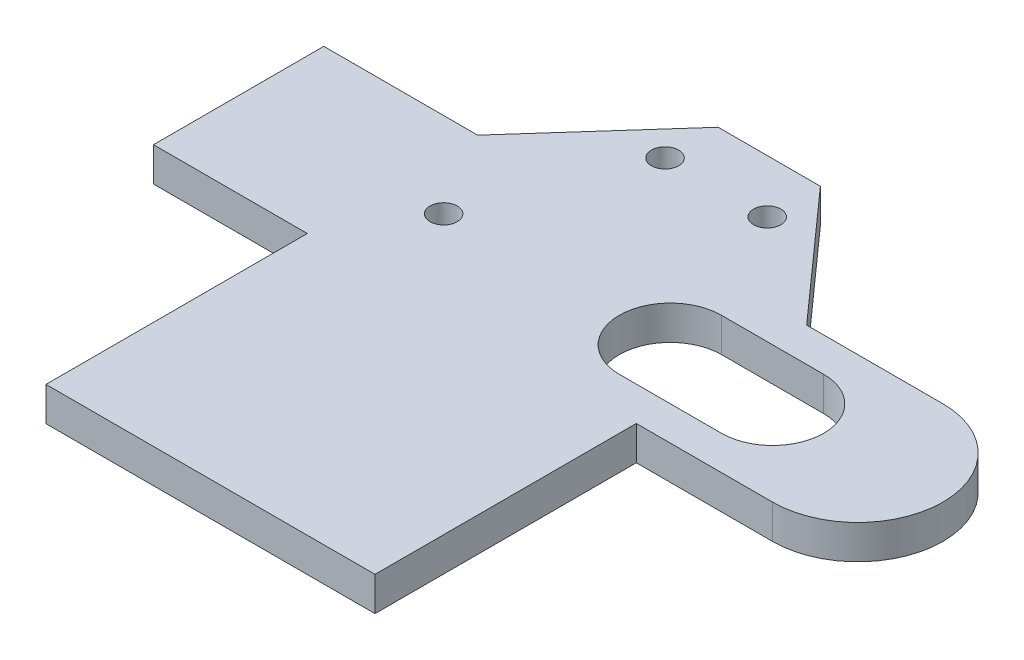
SolidWorks part; units mm, degrees
material "Epoxy, Unfilled"
ref_plane "Front Plane" through (0, 0, 0) normal (0, 0, 1) x (1, 0, 0)
ref_plane "Top Plane" through (0, 0, 0) normal (0, 1, 0) x (1, 0, 0)
ref_plane "Right Plane" through (0, 0, 0) normal (1, 0, 0) x (0, 0, -1)
sketch "Sketch1" plane through (0, 0, 0) normal (0, 1, 0) x (1, 0, 0)
  line L2 (-28.2843, 28.2843) -> (-28.2843, -48.4157)
  line L3 (-28.2843, 78.2843) -> (5, 115.5959)
  line L4 (5, 115.5959) -> (35, 115.5959)
  line L5 (35, 115.5959) -> (68.2843, 78.2843)
  line L6 (68.2843, 78.2843) -> (108.2843, 78.2843)
  line L7 (108.2843, 28.2843) -> (68.2843, 28.2843)
  line L9 (108.2843, 53.2843) -> (-28.2843, 53.2843) construction
  line L10 (20, 115.5959) -> (20, 0) construction
  line L11 (53.2843, 53.2843) -> (83.2843, 53.2843) construction
  line L12 (53.2843, 68.2843) -> (83.2843, 68.2843)
  line L13 (53.2843, 38.2843) -> (83.2843, 38.2843)
  line L14 (68.2843, 28.2843) -> (68.2843, 78.2843) construction
  line L15 (68.2843, 68.2843) -> (68.2843, 38.2843) construction
  line L16 (-28.2843, 78.2843) -> (-73.4393, 78.2843)
  line L17 (-73.4393, 78.2843) -> (-73.4393, 28.2843)
  line L18 (-73.4393, 28.2843) -> (-28.2843, 28.2843)
  line L19 (-28.2843, -48.4157) -> (63.3386, -48.4157)
  line L20 (63.3386, -48.4157) -> (68.2843, -48.4157)
  line L21 (68.2843, -48.4157) -> (68.2843, 28.2843)
  arc A0 (108.2843, 78.2843) -> (108.2843, 28.2843) centre (108.2843, 53.2843) cw
  circle A1 centre (5, 100) radius 4
  circle A2 centre (35, 100) radius 4
  circle A3 centre (-13.2843, 53.2843) radius 4
  arc A4 (53.2843, 68.2843) -> (53.2843, 38.2843) centre (53.2843, 53.2843) ccw
  arc A5 (83.2843, 38.2843) -> (83.2843, 68.2843) centre (83.2843, 53.2843) ccw
  point P23 (68.2843, 53.2843)
  dimension "D8" = 8
  dimension "D2" = 50
  dimension "D3" = 30
  dimension "D5" = 50
  dimension "D7" = 40
  dimension "D11" = 30
  dimension "D12" = 30
  dimension "D13" = 30
extrude "Boss-Extrude1" add sketch "Sketch1" along normal blind 10
sketch "Sketch2" plane through (0, 10, 0) normal (0, 1, 0) x (1, 0, 0)
  line L0 (68.2843, 68.2843) -> (68.2843, 38.2843) construction
  line L1 (83.2843, 68.2843) -> (53.2843, 68.2843) construction
  line L2 (53.2843, 38.2843) -> (83.2843, 38.2843) construction
ref_plane "Plane1" through (68.2843, 0, 0) normal (-1, 0, 0) x (0, 0, 1)
scale "Scale1" scale about centroid uniform scaling yes scale factor 0.5
